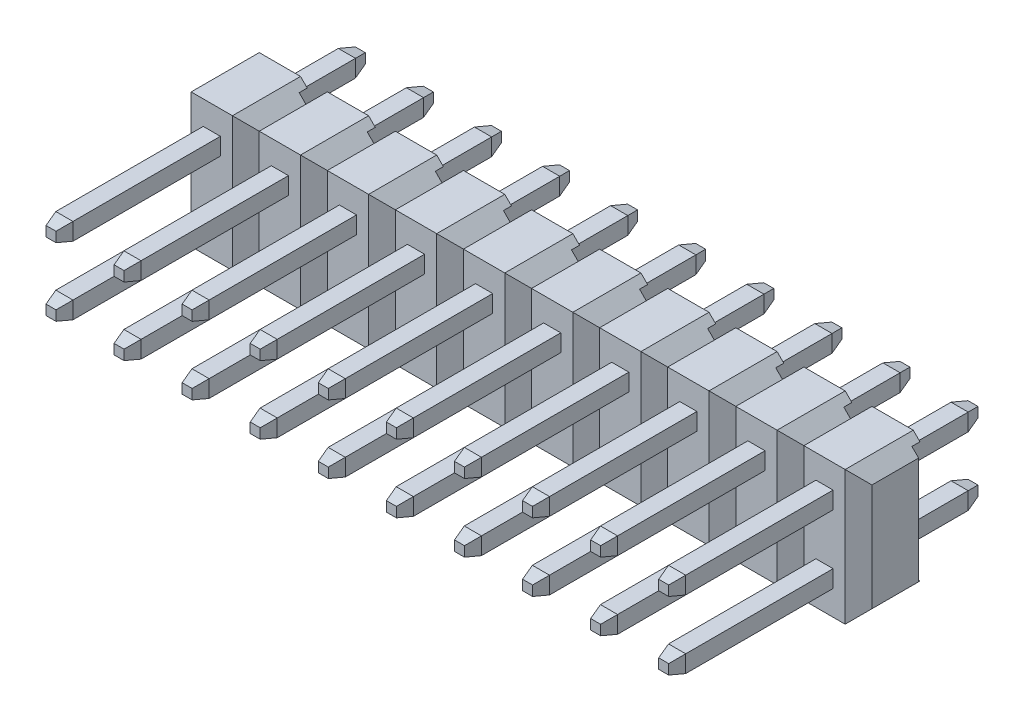
SolidWorks part; units mm, degrees
ref_plane "Front Plane" through (0, 0, 0) normal (0, 0, 1) x (1, 0, 0)
ref_plane "Top Plane" through (0, 0, 0) normal (0, 1, 0) x (1, 0, 0)
ref_plane "Right Plane" through (0, 0, 0) normal (1, 0, 0) x (0, 0, -1)
sketch "Sketch2" plane through (0, 0, 0) normal (0, 0, 1) x (1, 0, 0)
  line L1 (0, 0) -> (2.54, 0)
  line L2 (0, 0) -> (0, 5)
  line L3 (0, 5) -> (2.54, 5)
  line L4 (2.54, 0) -> (2.54, 5)
  dimension "length" = 2.54
  dimension "width" = 5
extrude "Boss-Extrude1" add sketch "Sketch2" along normal blind 2.54
sketch "Sketch3" plane through (0, 0, 0) normal (-1, 0, 0) x (0, 0, 1)
  line L0 (0, 2.5) -> (2.54, 2.5) construction
  line L1 (0, 5) -> (0, 0) construction
  line L2 (2.54, 5) -> (2.54, 0) construction
  line L3 (2.54, 5) -> (0, 5) construction
  line L4 (0, 4.75) -> (0.3, 4.75)
  line L5 (0, 4.75) -> (0, 0.25)
  line L6 (0, 0.25) -> (0.3, 0.25)
  line L7 (0.3, 4.75) -> (0.3, 0.25)
  point P10 (0, 2.5)
  dimension "D1" = 0.25
  dimension "D2" = 0.3
extrude "Cut-Extrude1" cut sketch "Sketch3" against normal through all
chamfer "Chamfer1" distance 0.5 angle 45 4 edges at (2.54, 5, 1.27) (2.54, 0, 1.27) (0, 5, 1.27) (0, 0, 1.27)
chamfer "Chamfer2" distance 0.5 angle 45 2 edges at (2.54, 2.5, 2.54) (0, 2.5, 2.54)
sketch "Sketch4" plane through (0, 0, 2.54) normal (0, 0, 1) x (1, 0, 0)
  line L0 (0.5, 1.25) -> (2.04, 1.25) construction
  line L1 (0.5, 5) -> (0.5, 0) construction
  line L2 (2.04, 0) -> (2.04, 5) construction
  line L3 (0.5, 0) -> (2.04, 0) construction
  line L4 (1.27, 5) -> (1.27, 0) construction
  line L5 (2.04, 5) -> (0.5, 5) construction
  line L7 (0.95, 1.57) -> (1.59, 1.57)
  line L8 (0.95, 1.57) -> (0.95, 0.93)
  line L9 (0.95, 0.93) -> (1.59, 0.93)
  line L10 (1.59, 1.57) -> (1.59, 0.93)
  point P16 (1.59, 1.25)
  point P17 (1.27, 1.57)
  dimension "D1" = 1.25
  dimension "D2" = 0.64
extrude "Boss-Extrude2" add sketch "Sketch4" along normal blind 6 separate body
sketch "Sketch6" plane through (0, 0, 0.3) normal (0, 0, -1) x (-1, 0, 0)
  line L1 (-1.59, 1.57) -> (-0.95, 1.57)
  line L2 (-1.59, 1.57) -> (-1.59, 0.93)
  line L3 (-1.59, 0.93) -> (-0.95, 0.93)
  line L4 (-0.95, 1.57) -> (-0.95, 0.93)
extrude "Boss-Extrude3" add sketch "Sketch6" along normal blind 3.3 separate body
chamfer "Chamfer3" distance 0.5 angle 15 4 edges at (1.27, 1.57, 8.54) (1.59, 1.25, 8.54) (1.27, 0.93, 8.54) (0.95, 1.25, 8.54)
chamfer "Chamfer4" distance 0.5 angle 15 4 edges at (1.27, 1.57, -3) (0.95, 1.25, -3) (1.27, 0.93, -3) (1.59, 1.25, -3)
pattern_linear "LPattern11" count 2 spacing 2.54 along (0, 1, 0) of bodies 104 103
pattern_linear "LPattern12" count 10 spacing 2.54 along (-1, 0, 0) of bodies 102
pattern_linear "LPattern13" count 10 spacing 2.54 along (-1, 0, 0) of bodies 104 110 103 111
equation "\"pins\"= 10"
equation "\"rows\"= 2"
equation "\"width@Sketch2\"= \"rows\" * 2.5"
equation "\"D1@LPattern11\"= \"rows\""
equation "\"D1@LPattern12\"= \"pins\""
equation "\"D1@LPattern11\"=\"rows\""
equation "\"D1@LPattern13\"=\"pins\""
